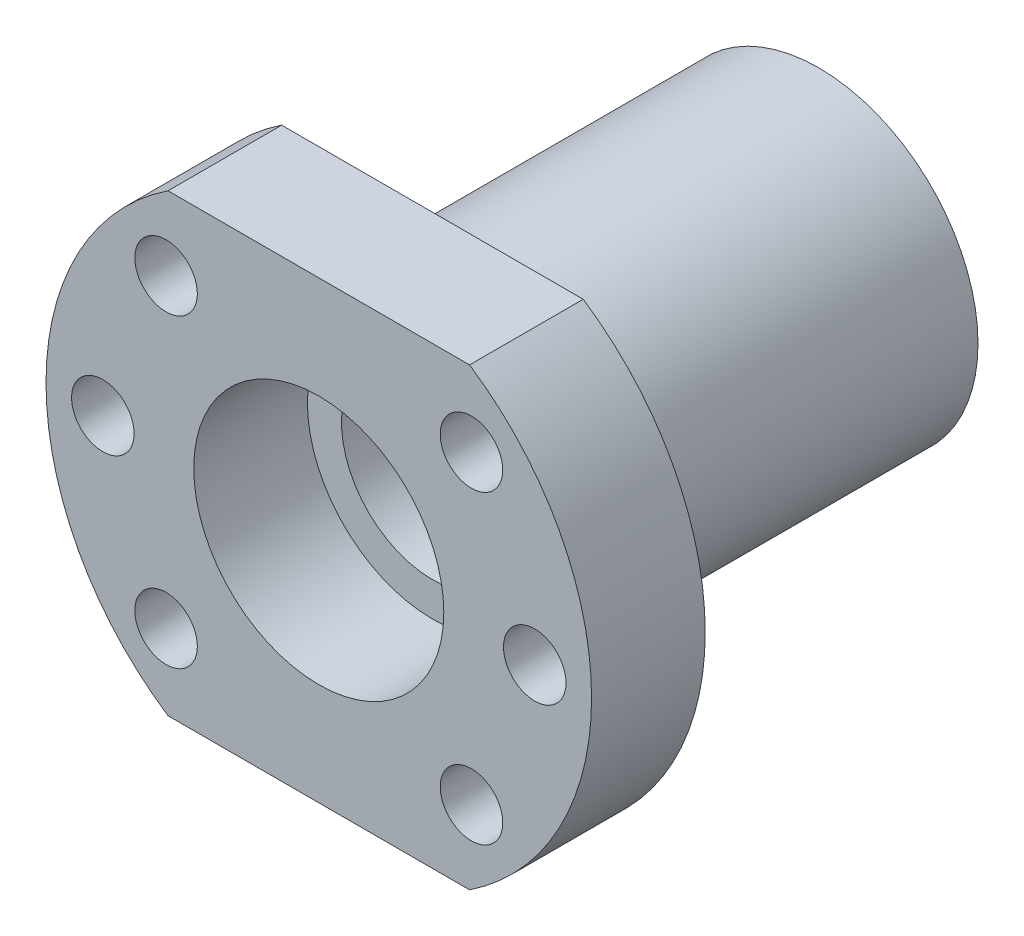
SolidWorks part; units mm, degrees
material "Plain Carbon Steel"
ref_plane "Front Plane" through (0, 0, 0) normal (0, 0, 1) x (1, 0, 0)
ref_plane "Top Plane" through (0, 0, 0) normal (0, 1, 0) x (1, 0, 0)
ref_plane "Right Plane" through (0, 0, 0) normal (1, 0, 0) x (0, 0, -1)
sketch "Sketch4" plane through (0, 0, 0) normal (1, 0, 0) x (0, 0, -1)
  line L0 (0, 0) -> (0, 11) construction
  line L1 (22, 11) -> (12, 11)
  line L2 (-22, 11) -> (-22, 24)
  line L3 (-22, 24) -> (-12, 24)
  line L4 (-12, 24) -> (-12, 14)
  line L5 (-12, 14) -> (22, 14)
  line L6 (22, 14) -> (22, 11)
  line L7 (-17.9283, 0) -> (16.6653, 0) construction
  line L8 (-12, 11) -> (-22, 11)
  line L9 (-12, 11) -> (12, 11) construction
  line L10 (-12, 11) -> (-12, 8)
  line L11 (-12, 8) -> (12, 8)
  line L12 (12, 11) -> (12, 8)
  dimension "D1" = 24
  dimension "D2" = 28
  dimension "D3" = 10
  dimension "D4" = 34
  dimension "D5" = 22
  dimension "D6" = 22
  dimension "D7" = 8
  dimension "D8" = 10
revolve "Revolve2" add sketch "Sketch4" angle 360 about L7
sketch "Sketch5" plane through (0, 0, 22) normal (0, 0, 1) x (1, 0, 0)
  line L0 (0, 35.9904) -> (0, 19.305) construction
  line L1 (-28.3026, 0) -> (22.4371, 0) construction
  line L2 (20, 20) -> (-20, 20)
  line L3 (20, 20) -> (20, 30)
  line L4 (20, 30) -> (-20, 30)
  line L5 (-20, 20) -> (-20, 30)
  line L6 (20, 20) -> (-20, 30) construction
  line L7 (20, 30) -> (-20, 20) construction
  line L8 (20, -20) -> (20, -30)
  line L9 (20, -20) -> (-20, -20)
  line L10 (-20, -20) -> (-20, -30)
  line L11 (20, -30) -> (-20, -30)
  point P1 (0, 25)
  dimension "D1" = 40
  dimension "D2" = 20
  dimension "D3" = 10
extrude "Cut-Extrude3" cut sketch "Sketch5" against normal through all
sketch "Sketch6" plane through (0, 0, 22) normal (0, 0, 1) x (1, 0, 0)
  line L0 (0, 0) -> (-19, 0) construction
  circle A0 centre (-19, 0) radius 2.75
  circle A1 centre (-13.435, 13.435) radius 2.75
  circle A2 centre (0, 19) radius 2.75 construction
  circle A3 centre (13.435, 13.435) radius 2.75
  circle A4 centre (19, 0) radius 2.75
  circle A5 centre (13.435, -13.435) radius 2.75
  circle A6 centre (0, -19) radius 2.75 construction
  circle A7 centre (-13.435, -13.435) radius 2.75
  point P20 (0, 0)
  dimension "D1" = 5.5
  dimension "D2" = 19
  dimension "D3" = 8
extrude "Cut-Extrude4" cut sketch "Sketch6" against normal through all
